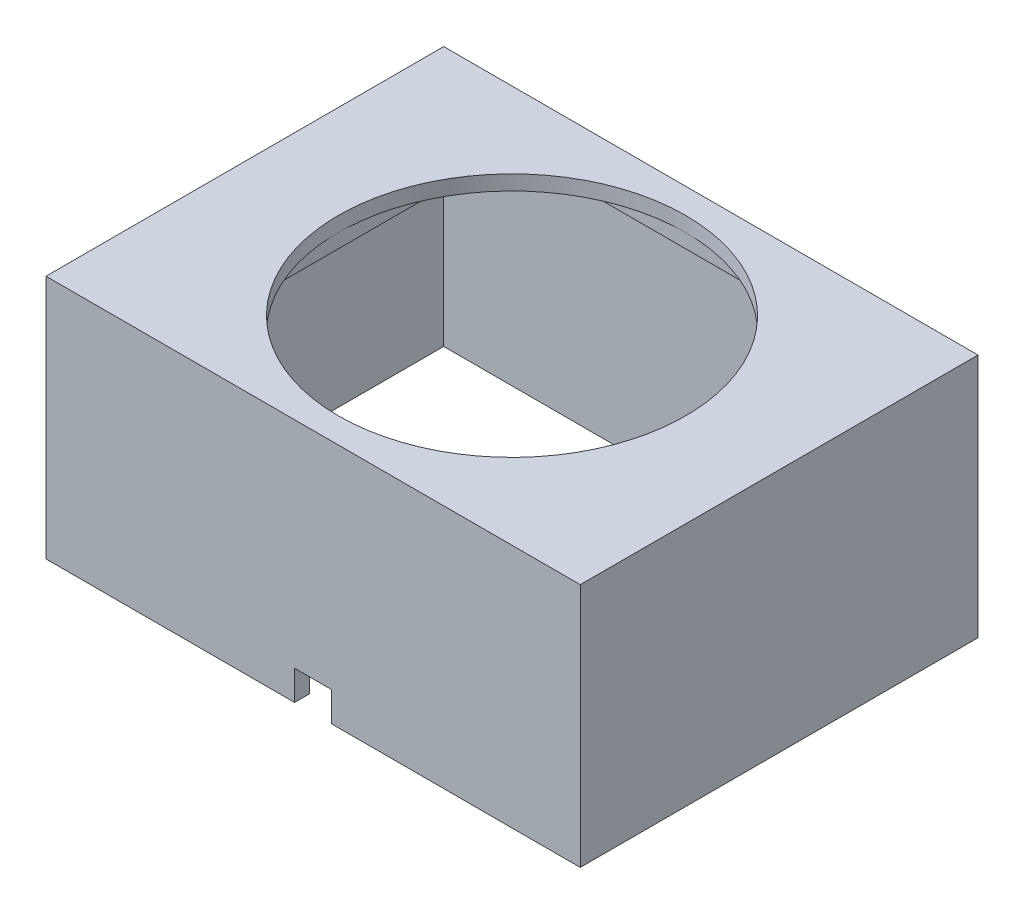
SolidWorks part; units mm, degrees
ref_plane "前视基准面" through (0, 0, 0) normal (0, 0, 1) x (1, 0, 0)
ref_plane "上视基准面" through (0, 0, 0) normal (0, 1, 0) x (1, 0, 0)
ref_plane "右视基准面" through (0, 0, 0) normal (1, 0, 0) x (0, 0, -1)
sketch "外外壳轮廓" plane through (0, 0, 0) normal (0, 1, 0) x (1, 0, 0)
  line L1 (-18, 13.4) -> (18, 13.4)
  line L2 (-18, 13.4) -> (-18, -13.4)
  line L3 (-18, -13.4) -> (18, -13.4)
  line L4 (18, 13.4) -> (18, -13.4)
  line L5 (-18, 13.4) -> (18, -13.4) construction
  line L6 (-18, -13.4) -> (18, 13.4) construction
  point P0 (0, 0)
  dimension "D1" = 36
  dimension "D2" = 26.8
extrude "凸台-拉伸1" add sketch "外外壳轮廓" along normal blind 16.5 contours L1 L4 L3 L2
ref_plane "基准面4" through (0, 0, 0) normal (0, -1, 0) x (-1, 0, 0)
sketch "外壳凹进" plane through (0, 0, 0) normal (0, -1, 0) x (-1, 0, 0)
  line L0 (18, -13.4) -> (-18, -13.4) construction
  line L1 (17, -12.4) -> (-17, -12.4)
  line L2 (17, -12.4) -> (17, 12.4)
  line L3 (17, 12.4) -> (-17, 12.4)
  line L4 (-17, -12.4) -> (-17, 12.4)
  line L5 (17, -12.4) -> (-17, 12.4) construction
  line L6 (17, 12.4) -> (-17, -12.4) construction
  line L7 (18, 13.4) -> (-18, 13.4) construction
  line L8 (18, 13.4) -> (18, -13.4) construction
  line L10 (-18, 13.4) -> (-18, -13.4) construction
  point P0 (0, 0)
  dimension "D1" = 1
  dimension "D2" = 1
  dimension "D3" = 1
  dimension "D4" = 1
extrude "切除-拉伸1" cut sketch "外壳凹进" against normal blind 14.5
sketch "草图4" plane through (0, 14.5, 0) normal (0, -1, 0) x (1, 0, 0)
  line L0 (17, -12.4) -> (17, 12.4) construction
  line L1 (-11.75, 11.75) -> (11.75, 11.75)
  line L2 (-11.75, 11.75) -> (-11.75, -11.75)
  line L3 (-11.75, -11.75) -> (11.75, -11.75)
  line L4 (11.75, 11.75) -> (11.75, -11.75)
  line L5 (-11.75, 11.75) -> (11.75, -11.75) construction
  line L6 (-11.75, -11.75) -> (11.75, 11.75) construction
  line L7 (-17, 12.4) -> (-17, -12.4) construction
  point P0 (0, 0)
  dimension "D1" = 23.5
  dimension "D2" = 23.5
  dimension "D3" = 5.25
  dimension "D4" = 5.25
extrude "切除-拉伸2" cut sketch "草图4" against normal blind 1 contours L2 L3 L4 L1
sketch "草图5" plane through (0, 15.5, 0) normal (0, -1, 0) x (1, 0, 0)
  circle A0 centre (0, 0) radius 11.7
  dimension "D1" = 23.4
extrude "切除-拉伸3" cut sketch "草图5" against normal blind 6 contours A0
ref_plane "基准面9" through (0, 16.5, 0) normal (0, 1, 0) x (1, 0, 0)
ref_plane "基准面10" through (0, 0, 0) normal (0, -1, 0) x (-1, 0, 0)
sketch "草图11" plane through (0, 0, 0) normal (0, -1, 0) x (-1, 0, 0)
  line L0 (18, -11.088) -> (-18, -11.088) construction
  line L1 (18, 13.4) -> (18, -13.4) construction
  line L2 (-18, 13.4) -> (-18, -13.4) construction
  line L3 (0, -11.088) -> (0, -20.1667) construction
  line L4 (18, -13.4) -> (-18, -13.4) construction
  line L5 (1.25, -13.4) -> (-1.25, -13.4)
  line L6 (1.25, -13.4) -> (1.25, -12.4)
  line L7 (1.25, -12.4) -> (-1.25, -12.4)
  line L8 (-1.25, -13.4) -> (-1.25, -12.4)
  line L9 (1.25, -13.4) -> (-1.25, -12.4) construction
  line L10 (1.25, -12.4) -> (-1.25, -13.4) construction
  line L11 (-17, -12.4) -> (17, -12.4) construction
  point P9 (0, -12.9)
  dimension "D1" = 2.5
extrude "切除-拉伸6" cut sketch "草图11" against normal blind 2 contours L6 L5 L8 L7
